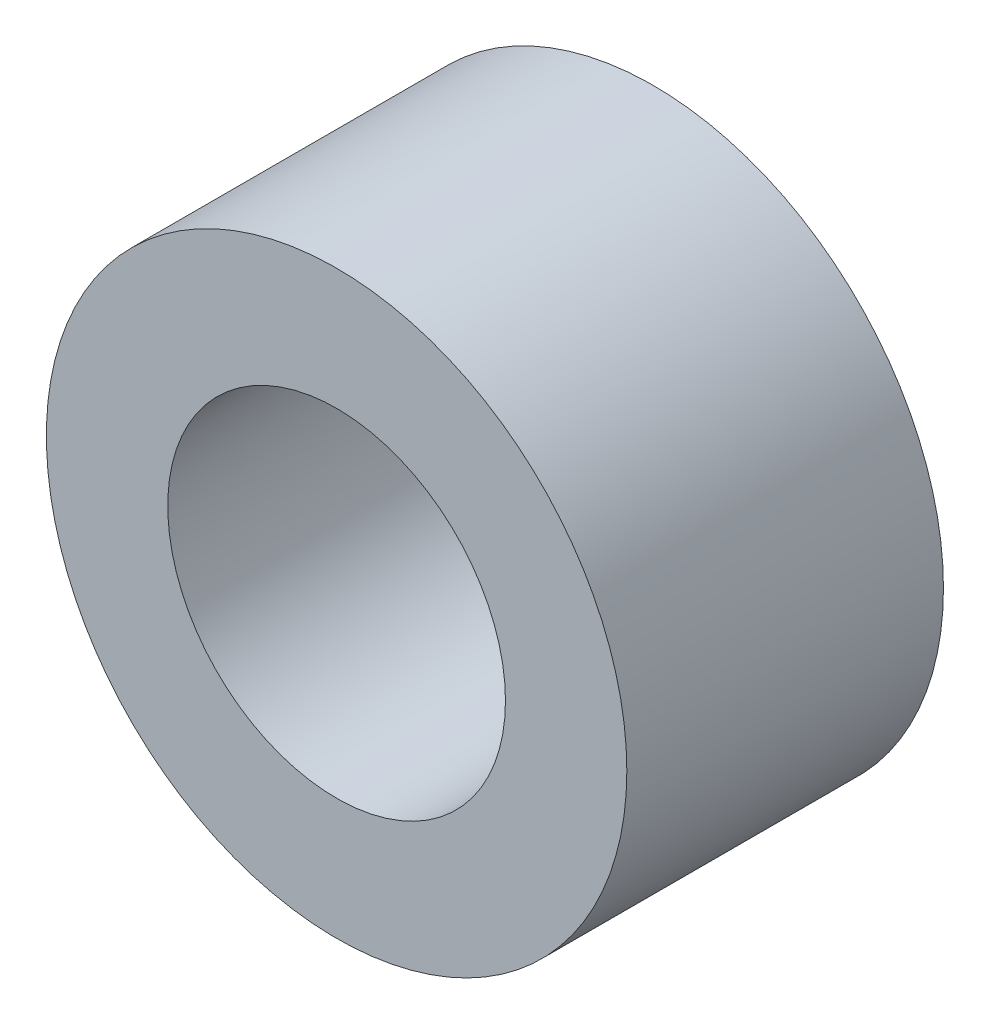
SolidWorks part; units mm, degrees
material "PA6"
ref_plane "Face" through (0, 0, 0) normal (0, 0, 1) x (1, 0, 0)
ref_plane "Dessus" through (0, 0, 0) normal (0, 1, 0) x (1, 0, 0)
ref_plane "Droite" through (0, 0, 0) normal (1, 0, 0) x (0, 0, -1)
sketch "Esquisse1" plane through (0, 0, 0) normal (0, 0, 1) x (1, 0, 0)
  circle A0 centre (0, 0) radius 1.6
  circle A1 centre (0, 0) radius 2.75
  dimension "D1" = 3.2
  dimension "D2" = 5.5
extrude "Boss.-Extru.1" add sketch "Esquisse1" along normal blind 3
